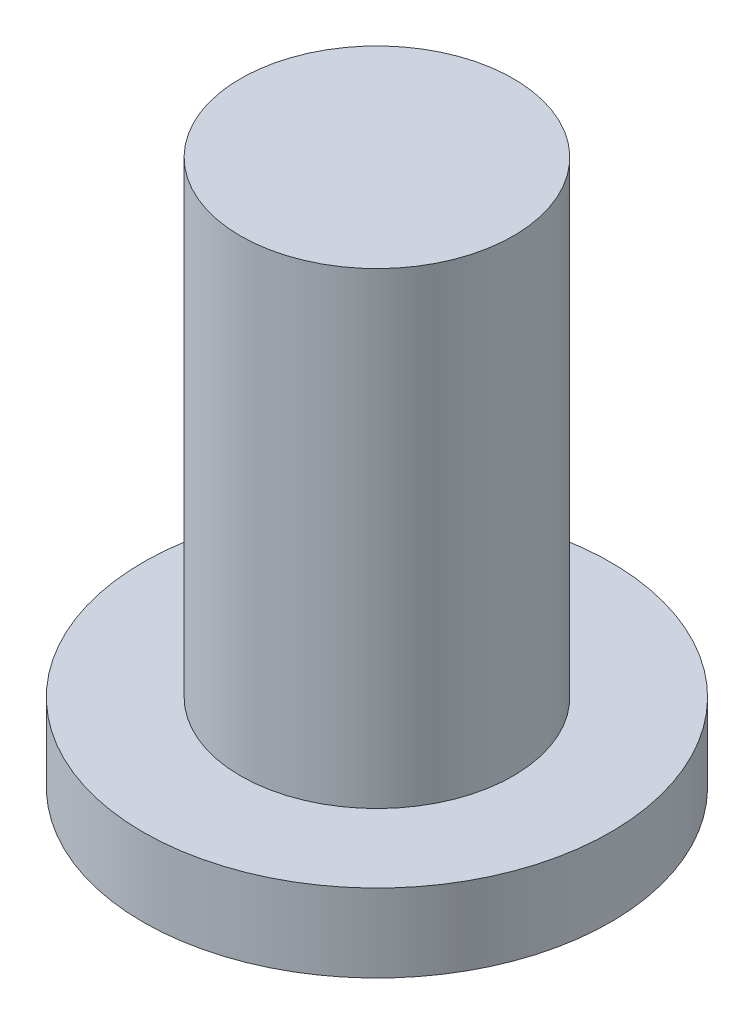
SolidWorks part; units mm, degrees
ref_plane "Alzado" through (0, 0, 0) normal (0, 0, 1) x (1, 0, 0)
ref_plane "Planta" through (0, 0, 0) normal (0, 1, 0) x (1, 0, 0)
ref_plane "Vista lateral" through (0, 0, 0) normal (1, 0, 0) x (0, 0, -1)
sketch "Croquis1" plane through (0, 0, 0) normal (0, 1, 0) x (1, 0, 0)
  circle A0 centre (0, 0) radius 6
  dimension "D1" = 12
extrude "Saliente-Extruir1" add sketch "Croquis1" along normal blind 2
sketch "Croquis2" plane through (0, 2, 0) normal (0, 1, 0) x (1, 0, 0)
  circle A0 centre (0, 0) radius 3.5
  dimension "D1" = 7
extrude "Saliente-Extruir2" add sketch "Croquis2" along normal blind 12
